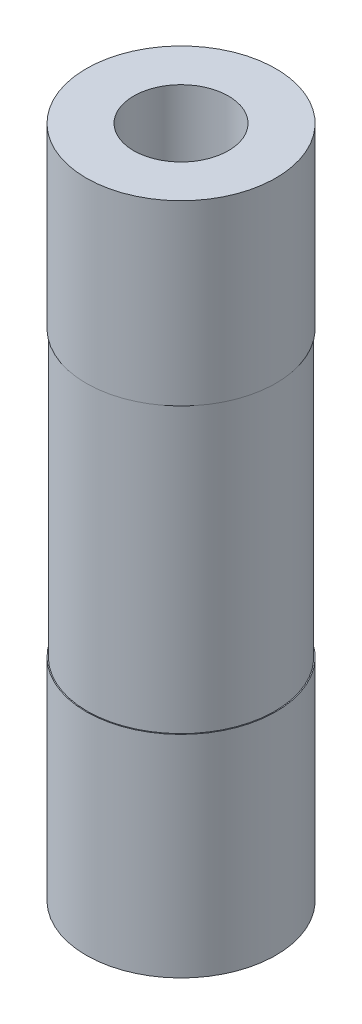
SolidWorks part; units mm, degrees
ref_plane "Alzado" through (0, 0, 0) normal (0, 0, 1) x (1, 0, 0)
ref_plane "Planta" through (0, 0, 0) normal (0, 1, 0) x (1, 0, 0)
ref_plane "Vista lateral" through (0, 0, 0) normal (1, 0, 0) x (0, 0, -1)
sketch "Croquis1" plane through (0, 0, 0) normal (0, 1, 0) x (1, 0, 0)
  circle A0 centre (0, 0) radius 10
  dimension "D1" = 20
extrude "Saliente-Extruir1" add sketch "Croquis1" along normal blind 71
sketch "Croquis2" plane through (0, 71, 0) normal (0, 1, 0) x (1, 0, 0)
  circle A0 centre (0, 0) radius 5
  dimension "D1" = 10
extrude "Cortar-Extruir1" cut sketch "Croquis2" against normal through all
sketch "Croquis3" plane through (0, 0, 0) normal (1, 0, 0) x (0, 0, -1)
  line L0 (10, 0) -> (10, 71) construction
  line L1 (10, 22.25) -> (9.9, 22.25)
  line L2 (10, 22.25) -> (10, 52.25)
  line L3 (10, 52.25) -> (9.9, 52.25)
  line L4 (9.9, 22.25) -> (9.9, 52.25)
  line L5 (10, 71) -> (-10, 71) construction
  line L6 (0, 71) -> (0, 19.3362) construction
  point P6 (9.95, 52.25)
  dimension "D1" = 30
  dimension "D2" = 18.75
  dimension "D3" = 0.1
revolve "Cortar-Revolución1" cut sketch "Croquis3" angle 360 about L6
